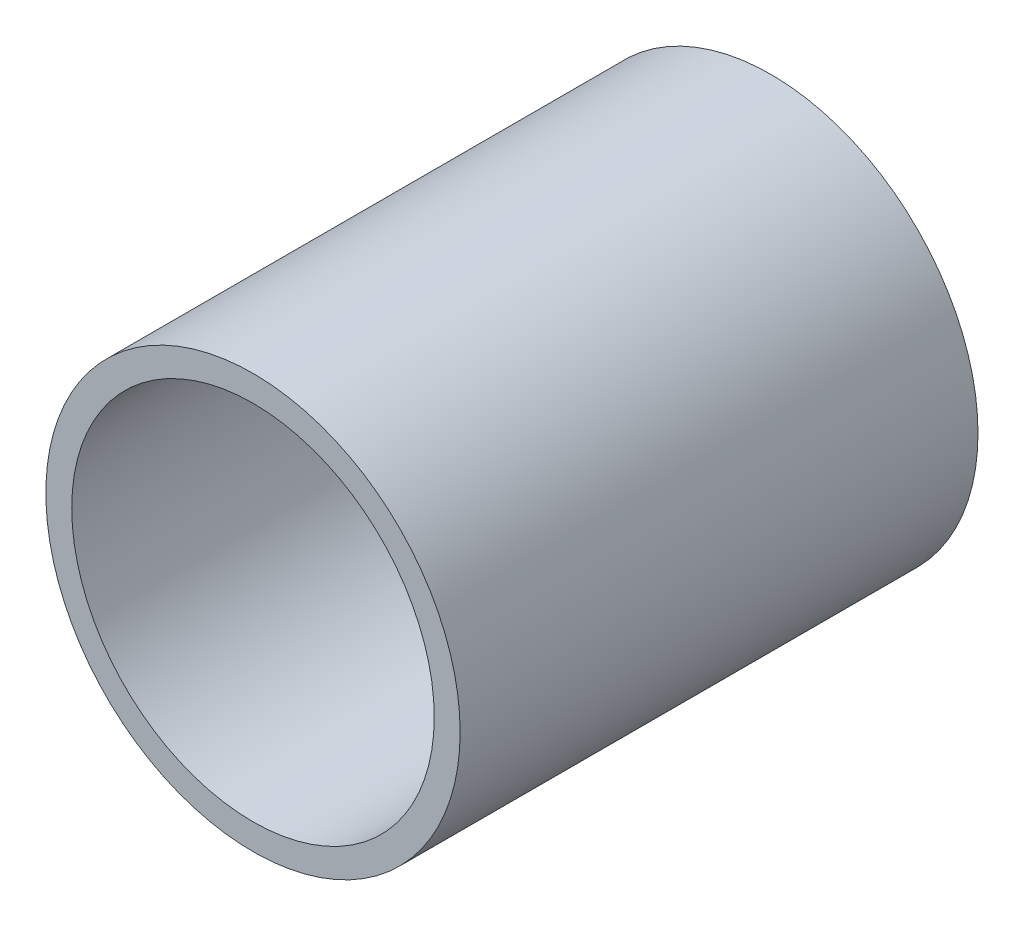
SolidWorks part; units mm, degrees
ref_plane "Спереди" through (0, 0, 0) normal (0, 0, 1) x (1, 0, 0)
ref_plane "Сверху" through (0, 0, 0) normal (0, 1, 0) x (1, 0, 0)
ref_plane "Справа" through (0, 0, 0) normal (1, 0, 0) x (0, 0, -1)
sketch "Эскиз1" plane through (0, 0, 0) normal (0, 0, 1) x (1, 0, 0)
  circle A0 centre (0, 0) radius 16
extrude "Бобышка-Вытянуть1" add sketch "Эскиз1" along normal blind 40
sketch "Эскиз2" plane through (0, 0, 0) normal (0, 0, -1) x (-1, 0, 0)
  circle A0 centre (0, 0) radius 14
extrude "Вырез-Вытянуть1" cut sketch "Эскиз2" against normal through all
